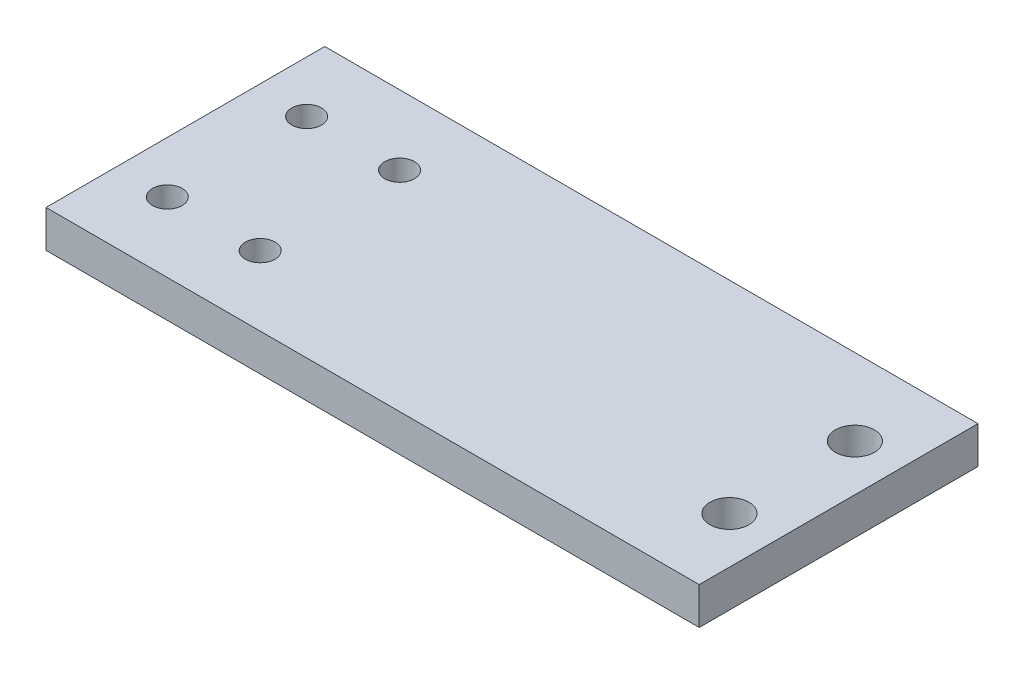
SolidWorks part; units mm, degrees
ref_plane "前视基准面" through (0, 0, 0) normal (0, 0, 1) x (1, 0, 0)
ref_plane "上视基准面" through (0, 0, 0) normal (0, 1, 0) x (1, 0, 0)
ref_plane "右视基准面" through (0, 0, 0) normal (1, 0, 0) x (0, 0, -1)
sketch "草图1" plane through (0, 0, 0) normal (0, 1, 0) x (1, 0, 0)
  line L0 (-29.7265, 7.998) -> (14.8464, 7.998) construction
  line L1 (14.8464, 7.998) -> (86.1037, 7.998) construction
  line L2 (46.5518, 22.998) -> (46.5518, -7.002)
  line L3 (46.5518, -7.002) -> (-23.7482, -7.002)
  line L4 (-23.7482, -7.002) -> (-23.7482, 22.998)
  line L5 (46.5518, 22.998) -> (-23.7482, 22.998)
  circle A0 centre (-18.1955, 15.498) radius 1.6
  circle A1 centre (-18.1955, 0.498) radius 1.6
  circle A2 centre (-8.1955, 15.498) radius 1.6
  circle A3 centre (-8.1955, 0.498) radius 1.6
  circle A4 centre (41.5518, 14.748) radius 2.1
  circle A5 centre (41.5518, 1.248) radius 2.1
  point P20 (46.5518, 7.998)
  point P21 (-23.7482, 7.998)
  dimension "D1" = 10
  dimension "D2" = 3.2
  dimension "D3" = 3.2
  dimension "D4" = 3.2
  dimension "D5" = 3.2
  dimension "D9" = 70.3
  dimension "D6" = 15
  dimension "D7" = 7.5
  dimension "D8" = 7.5
  dimension "D10" = 6.75
  dimension "D11" = 5
  dimension "D12" = 15
  dimension "D13" = 5.5527
  dimension "D14" = 10
extrude "凸台-拉伸1" add sketch "草图1" along normal blind 4
sketch "草图3" plane through (0, 4, 0) normal (0, 1, 0) x (1, 0, 0)
  line L0 (-8.1955, 15.498) -> (-8.1955, 0.498) construction
  line L1 (-8.1955, 7.998) -> (14.5156, 7.998) construction
sketch "草图4" plane through (0, 0, 0) normal (0, -1, 0) x (1, 0, 0)
  line L0 (-8.1955, -0.498) -> (-8.1955, -15.498) construction
  line L1 (-8.1955, -7.998) -> (17.1433, -7.998) construction
